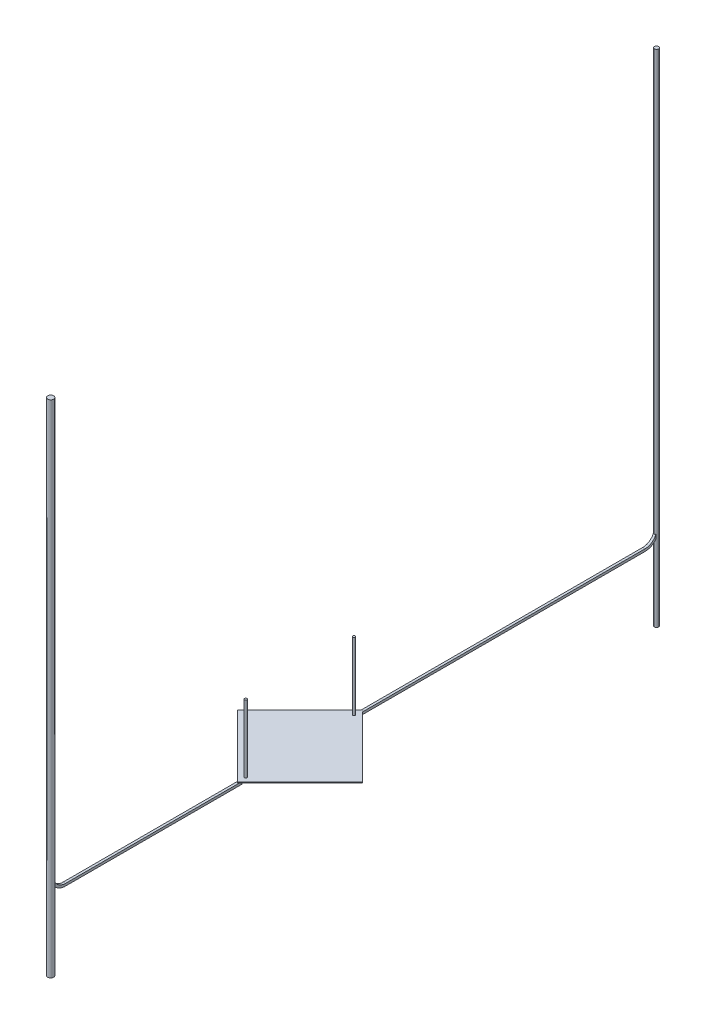
SolidWorks part; units mm, degrees
material "电源线路板"
ref_plane "前视基准面" through (0, 0, 0) normal (0, 0, 1) x (1, 0, 0)
ref_plane "上视基准面" through (0, 0, 0) normal (0, 1, 0) x (1, 0, 0)
ref_plane "右视基准面" through (0, 0, 0) normal (1, 0, 0) x (0, 0, -1)
sketch "草图1" plane through (0, 0, 0) normal (0, 1, 0) x (1, 0, 0)
  line L0 (0, 0) -> (0, 15)
  line L1 (0, 15) -> (15, 15)
  line L2 (15, 15) -> (15, 0)
  line L3 (15, 0) -> (0, 0)
extrude "凸台-拉伸1" add sketch "草图1" along normal blind 0.1
sketch "草图2" plane through (0, 0.1, 0) normal (0, 1, 0) x (1, 0, 0)
  circle A0 centre (1, 1) radius 0.2
  circle A1 centre (14, 14) radius 0.2
extrude "凸台-拉伸2" add sketch "草图2" along normal blind 11.5 separate body
sketch "草图3" plane through (0, 0, 0) normal (0, -1, 0) x (1, 0, 0)
  line L0 (9.5, -14.5) -> (0.5, -14.5)
  line L1 (0.5, -14.5) -> (0.5, -0.5)
  line L2 (0.5, -0.5) -> (7.5, -0.5)
  line L3 (14.5, -14.5) -> (14.5, -9.5)
  line L4 (14.5, -9.5) -> (7.5, -9.5)
  line L5 (8.7, -0.5) -> (9.5, -0.5)
  line L6 (9.5, -14.5) -> (14.5, -14.5)
  line L7 (7.5, -0.5) -> (7.5, -9.5)
  line L9 (8.7, -0.5) -> (8.7, -3)
  line L10 (14.5, -0.5) -> (14.5, -3)
  line L11 (14.5, -3) -> (13.7, -3)
  line L12 (13.7, -3) -> (13.7, -0.5)
  line L13 (13.7, -0.5) -> (14.5, -0.5)
  line L14 (8.7, -3) -> (9.5, -3)
  line L15 (9.5, -3) -> (9.5, -0.5)
extrude "凸台-拉伸3" add sketch "草图3" along normal blind 0.05 separate body
sketch "草图4" plane through (0, 0, 0) normal (0, -1, 0) x (1, 0, 0)
  line L0 (13.7, -0.5) -> (9.5, -0.5)
  line L1 (9.5, -0.5) -> (9.5, -3)
  line L3 (9.5, -3) -> (13.7, -3)
  line L4 (13.7, -0.5) -> (13.7, -3) construction
  line L5 (13.7, -3) -> (13.7, -0.5)
extrude "凸台-拉伸4" add sketch "草图4" along normal blind 0.05 separate body
sketch "草图5" plane through (0, -0.05, 0) normal (0, -1, 0) x (1, 0, 0)
  circle A0 centre (9.1, -0.9) radius 0.1
extrude "凸台-拉伸5" add sketch "草图5" along normal blind 0.3
sketch "草图6" plane through (0, -0.35, 0) normal (0, -1, 0) x (1, 0, 0)
  line L1 (9.5, -0.5) -> (8.7, -0.5) construction
  line L2 (9.1, -0.5) -> (0.5, -0.5)
  line L3 (0.5, -0.5) -> (0.5, -14.5)
  line L4 (0.5, -14.5) -> (9.5, -14.5)
  line L5 (0.5, -14.5) -> (14.5, -14.5) construction
  line L6 (9.5, -14.5) -> (9.5, -0.5)
  line L7 (9.5, -0.5) -> (9.1, -0.5)
extrude "凸台-拉伸6" add sketch "草图6" along normal blind 0.05 separate body
sketch "草图7" plane through (0, -0.05, 0) normal (0, -1, 0) x (1, 0, 0)
  line L3 (13.5, -13.5) -> (12.5, -13.5)
  line L4 (12.5, -13.5) -> (12.5, -12.5)
  line L5 (12.5, -12.5) -> (13.5, -12.5)
  line L6 (13.5, -12.5) -> (13.5, -13.5)
extrude "凸台-拉伸7" add sketch "草图7" along normal blind 0.3 separate body
move or copy body "实体-移动/复制19" bodies to move or copy 109 106 115 108 114 112 113 107 111 copy no translate (-14, 0, 14)
move or copy body "实体-移动/复制20" bodies to move or copy 229 230 232 228 231 224 225 226 227 copy no rotation origin (0, 0, 0) rotation axis (0, 1, 0) rotation angle 45
sketch "草图27" plane through (0, 0, 0) normal (0, 1, 0) x (1, 0, 0)
  circle A0 centre (0, 51.35) radius 0.35
extrude "凸台-拉伸30" add sketch "草图27" along normal blind 72.5 separate body
sketch "草图28" plane through (0, 0, 0) normal (0, 1, 0) x (1, 0, 0)
  circle A0 centre (0, -51.5) radius 0.5
extrude "凸台-拉伸31" add sketch "草图28" along normal blind 72.5 separate body
sketch "草图29" plane through (0, 0, 0) normal (1, 0, 0) x (0, 0, -1)
  line L1 (0, 0) -> (49.2, 0)
  line L2 (0, 0) -> (0, -0.4)
  line L3 (0, -0.4) -> (49.2, -0.4)
  line L4 (49.2, 0) -> (49.2, -0.4)
  line L5 (0, 0) -> (49.2, -0.4) construction
  line L6 (0, -0.4) -> (49.2, 0) construction
  point P4 (24.6, -0.2)
extrude "凸台-拉伸32" add sketch "草图29" along normal mid plane 0.4
sketch "草图33" plane through (0, 0, 0) normal (1, 0, 0) x (0, 0, -1)
  line L0 (-19.799, 0) -> (-9.1924, 0) construction
  line L1 (-19.1952, 0) -> (-49.2, 0)
  line L2 (-19.1952, 0) -> (-19.1952, -0.4)
  line L3 (-19.1952, -0.4) -> (-49.2, -0.4)
  line L4 (-49.2, 0) -> (-49.2, -0.4)
  line L5 (-19.1952, 0) -> (-49.2, -0.4) construction
  line L6 (-19.1952, -0.4) -> (-49.2, 0) construction
  point P4 (-34.1976, -0.2)
extrude "凸台-拉伸34" add sketch "草图33" along normal mid plane 0.4
sketch "草图40" plane through (0, 0, -49.2) normal (0, 0, -1) x (-1, 0, 0)
  line L1 (-0.2, 0) -> (0.2, 0)
  line L2 (-0.2, 0) -> (-0.2, -0.4)
  line L3 (-0.2, -0.4) -> (0.2, -0.4)
  line L4 (0.2, 0) -> (0.2, -0.4)
  line L5 (-0.2, 0) -> (0.2, -0.4) construction
  line L6 (-0.2, -0.4) -> (0.2, 0) construction
  line L7 (-0.2, 0) -> (-0.4, 0)
  line L8 (-0.2, 0) -> (-0.2, 2)
  line L9 (-0.2, 2) -> (-0.4, 2)
  line L10 (-0.4, 0) -> (-0.4, 2)
  line L11 (-0.2, 0) -> (-0.4, 2) construction
  line L12 (-0.2, 2) -> (-0.4, 0) construction
  point P4 (0, -0.2)
  point P10 (-0.3, 1)
revolve "旋转1" add sketch "草图40" angle 90 about L9
sketch "草图41" plane through (0, 0, 49.2) normal (0, 0, 1) x (1, 0, 0)
  line L1 (-0.2, 0) -> (0.2, 0)
  line L2 (-0.2, 0) -> (-0.2, -0.4)
  line L3 (-0.2, -0.4) -> (0.2, -0.4)
  line L4 (0.2, 0) -> (0.2, -0.4)
  line L5 (-0.2, 0) -> (0.2, -0.4) construction
  line L6 (-0.2, -0.4) -> (0.2, 0) construction
  line L7 (-0.2, 0) -> (-0.4, 0)
  line L8 (-0.2, 0) -> (-0.2, 2)
  line L9 (-0.2, 2) -> (-0.4, 2)
  line L10 (-0.4, 0) -> (-0.4, 2)
  line L11 (-0.2, 0) -> (-0.4, 2) construction
  line L12 (-0.2, 2) -> (-0.4, 0) construction
  point P4 (0, -0.2)
  point P10 (-0.3, 1)
revolve "旋转2" add sketch "草图41" angle 90 about L9
sketch "草图43" plane through (0, 0, 0) normal (0, -1, 0) x (1, 0, 0)
  circle A0 centre (0, -51.35) radius 0.35
extrude "凸台-拉伸35" add sketch "草图43" along normal blind 12.5
sketch "草图44" plane through (0, 0, 0) normal (0, -1, 0) x (1, 0, 0)
  circle A0 centre (0, 51.5) radius 0.5
extrude "凸台-拉伸36" add sketch "草图44" along normal blind 12.5
